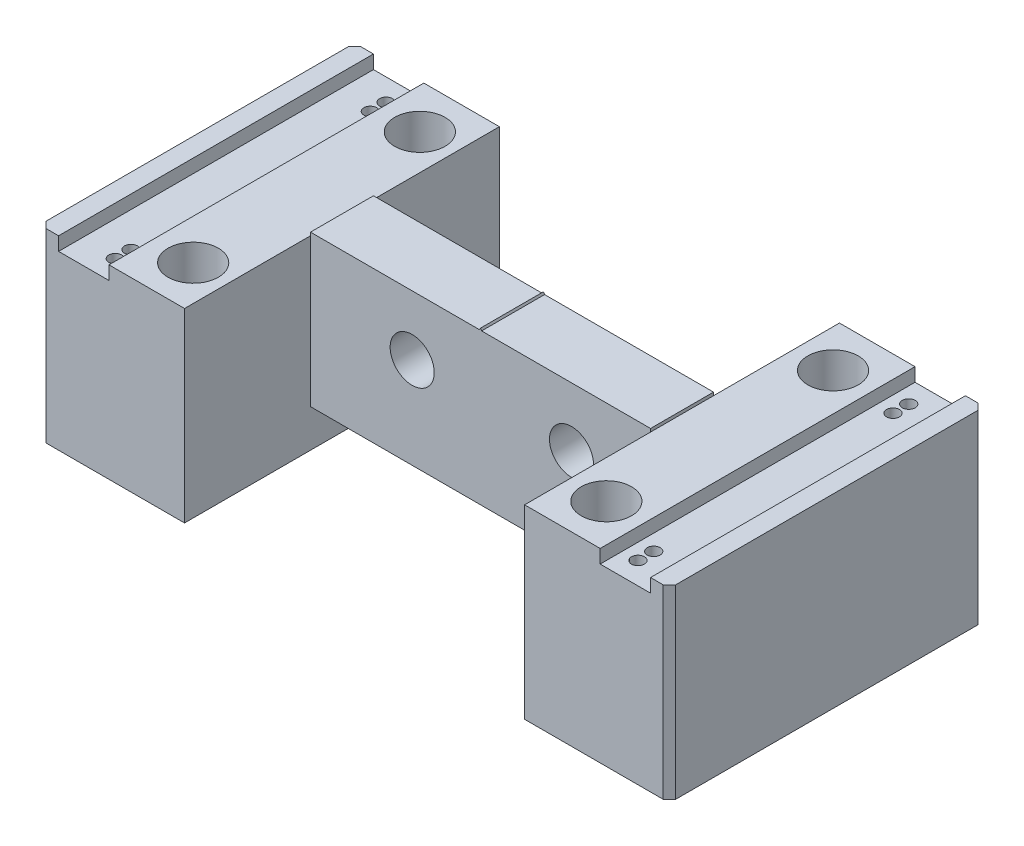
SolidWorks part; units mm, degrees
ref_plane "Front Plane" through (0, 0, 0) normal (0, 0, 1) x (1, 0, 0)
ref_plane "Top Plane" through (0, 0, 0) normal (0, 1, 0) x (1, 0, 0)
ref_plane "Right Plane" through (0, 0, 0) normal (1, 0, 0) x (0, 0, -1)
sketch "Sketch1" plane through (0, 0, 0) normal (0, 0, 1) x (1, 0, 0)
  line L0 (6.0135, 8.1149) -> (9.0135, 8.1149)
  line L1 (-13.9865, 8.1149) -> (-1.9865, 8.1149)
  line L2 (-13.9865, 8.1149) -> (-13.9865, -21.3851)
  line L3 (-13.9865, -21.3851) -> (9.0135, -21.3851)
  line L4 (9.0135, 8.1149) -> (9.0135, -21.3851)
  line L6 (-1.9865, 8.1149) -> (-1.9865, 5.9649)
  line L7 (-1.9865, 5.9649) -> (6.0135, 5.9649)
  line L8 (6.0135, 8.1149) -> (6.0135, 5.9649)
  dimension "D1" = 29.5
  dimension "D2" = 27.35
  dimension "D3" = 23
  dimension "D4" = 8
  dimension "D5" = 12
extrude "Boss-Extrude1" add sketch "Sketch1" along normal blind 50
sketch "Sketch2" plane through (-13.9865, 0, 0) normal (-1, 0, 0) x (0, 0, 1)
  line L0 (50, -21.3851) -> (0, -21.3851) construction
  line L1 (20, -21.3851) -> (30, -21.3851)
  line L2 (20, -21.3851) -> (20, 8.6149)
  line L3 (20, 8.6149) -> (30, 8.6149)
  line L4 (30, -21.3851) -> (30, 8.6149)
  line L5 (0, 8.1149) -> (0, -21.3851) construction
  line L6 (50, 8.1149) -> (50, -21.3851) construction
  dimension "D1" = 20
  dimension "D2" = 20
  dimension "D3" = 30
extrude "Boss-Extrude2" add sketch "Sketch2" along normal blind 54
sketch "Sketch3" plane through (0, 0, 20) normal (0, 0, -1) x (-1, 0, 0)
  line L0 (40.8115, 8.6149) -> (40.9865, 8.918)
  line L1 (67.9865, 8.6149) -> (13.9865, 8.6149) construction
  line L2 (40.9865, 8.918) -> (41.1615, 8.6149)
  line L8 (13.9865, 8.6149) -> (13.9865, 8.1149)
  line L9 (13.9865, 8.1149) -> (13.9865, -21.3851)
  line L10 (13.9865, -21.3851) -> (67.9865, -21.3851)
  line L11 (67.9865, -21.3851) -> (67.9865, 8.6149)
  line L12 (67.9865, 8.6149) -> (13.9865, 8.6149)
  line L17 (41.1615, 8.6149) -> (40.8115, 8.6149)
  point P4 (0, 0)
  point P6 (40.9865, 8.6149)
  point P7 (0, 0)
  dimension "D1" = 60
  dimension "D2" = 0.35
  dimension "D3" = 0
extrude "Boss-Extrude4" add sketch "Sketch3" against normal up to surface (10 mm away) up to face at (-35.5865, -3.4851, 30)
sketch "Sketch4" plane through (0, 0, 0) normal (0, 0, -1) x (-1, 0, 0)
  line L0 (67.9865, 8.6149) -> (67.9865, -21.3851) construction
  line L1 (67.9865, 8.1149) -> (79.9865, 8.1149)
  line L2 (67.9865, 8.1149) -> (67.9865, -21.3851)
  line L3 (67.9865, -21.3851) -> (90.9865, -21.3851)
  line L4 (90.9865, 8.1149) -> (90.9865, -21.3851)
  line L5 (87.9865, 8.1149) -> (90.9865, 8.1149)
  line L7 (79.9865, 8.1149) -> (79.9865, 5.9649)
  line L8 (79.9865, 5.9649) -> (87.9865, 5.9649)
  line L9 (87.9865, 8.1149) -> (87.9865, 5.9649)
  line L10 (-6.0135, 8.1149) -> (-6.0135, 5.9649) construction
  line L11 (-6.0135, 5.9649) -> (1.9865, 5.9649) construction
  line L13 (1.9865, 5.9649) -> (1.9865, 8.1149) construction
  line L14 (1.9865, 8.1149) -> (13.9865, 8.1149) construction
  line L15 (13.9865, -21.3851) -> (-9.0135, -21.3851) construction
  line L16 (-9.0135, -21.3851) -> (-9.0135, 8.1149) construction
  point P13 (0, 0)
extrude "Boss-Extrude5" add sketch "Sketch4" against normal blind 50
sketch "Sketch5" plane through (0, 0, 20) normal (0, 0, -1) x (-1, 0, 0)
  line L0 (67.9865, -21.3851) -> (13.9865, -21.3851) construction
  circle A0 centre (26.5372, -0.8851) radius 3.5
  circle A1 centre (51.8381, -0.8851) radius 3.5
  point P4 (0, 0)
  dimension "D2" = 7
  dimension "D1" = 20.5
extrude "Cut-Extrude1" cut sketch "Sketch5" against normal blind 54
sketch "Sketch6" plane through (0, 8.1149, 0) normal (0, 1, 0) x (1, 0, 0)
  circle A0 centre (-7.9819, -7.0264) radius 2.25
  circle A1 centre (-7.9819, -43.0216) radius 2.25
  circle A2 centre (-73.5937, -43.0216) radius 2.25
  circle A3 centre (-73.5937, -7.0264) radius 2.25
  point P8 (0, 0)
  point P9 (0, 0)
  point P10 (0, 0)
  point P11 (0, 0)
  point P12 (0, 0)
  dimension "D1" = 4.5
extrude "Cut-Extrude2" cut sketch "Sketch6" against normal through all
sketch "Sketch7" plane through (0, 8.1149, 0) normal (0, 1, 0) x (1, 0, 0)
  circle A0 centre (-7.9819, -43.0216) radius 4
  circle A1 centre (-7.9819, -7.0264) radius 4
  circle A2 centre (-73.5937, -43.0216) radius 4
  circle A3 centre (-73.5937, -7.0264) radius 4
  dimension "D1" = 8
extrude "Cut-Extrude3" cut sketch "Sketch7" against normal blind 10
hole_wizard "M2.5 Tapped Hole2" positions "Sketch12" profile "Sketch13" tap size "M2.5" standard "ISO"
sketch "Sketch12" plane through (0, 5.9649, 0) normal (0, 1, 0) x (1, 0, 0)
  line L0 (6.0135, -50) -> (-1.9865, -50) construction
  line L1 (9.0135, -50) -> (9.0135, 0) construction
  point P0 (0.5135, -46.5)
  point P2 (0.5135, -3.5)
  point P4 (-82.4865, -46.5)
  point P6 (-82.4865, -3.5)
  point P12 (0.5135, -44)
  point P14 (0.5135, -6)
  point P16 (-82.4865, -44)
  point P18 (-82.4865, -6)
  point P23 (0, 0)
  point P24 (0, 0)
  point P25 (0, 0)
  point P26 (0, 0)
  dimension "D1" = 3.5
  dimension "D2" = 6
  dimension "D3" = 44
  dimension "D4" = 46.5
  dimension "D5" = 8.5
  dimension "D6" = 91.5
sketch "Sketch13" plane through (0.5135, 5.9649, 46.5) normal (1, 0, 0) x (0, 0, 1)
  line L0 (0, 0) -> (0, 6.9659)
  line L1 (0, 6.9659) -> (1.025, 6.35)
  line L2 (1.025, 6.35) -> (1.025, 0)
  line L5 (1.025, 0) -> (0, 0)
  line L10 (0, 6.9659) -> (-1.025, 6.35) construction
  line L11 (0, -6.35) -> (0, 107.95) construction
  dimension "Tap Drill Dia." = 2.05
  dimension "Tap Drill Depth" = 6.35
  dimension "Drill Angle" = 118
cosmetic thread "Hole Thread5" parameters "D1"=5, "D2"=2.5
cosmetic thread "Hole Thread6" parameters "D1"=5, "D2"=2.5
cosmetic thread "Hole Thread7" parameters "D1"=5, "D2"=2.5
cosmetic thread "Hole Thread8" parameters "D1"=5, "D2"=2.5
cosmetic thread "Hole Thread9" parameters "D1"=5, "D2"=2.5
cosmetic thread "Hole Thread10" parameters "D1"=5, "D2"=2.5
cosmetic thread "Hole Thread11" parameters "D1"=5, "D2"=2.5
cosmetic thread "Hole Thread12" parameters "D1"=5, "D2"=2.5
chamfer "Chamfer1" distance 1 angle 45 4 edges at (-90.9865, -6.6351, 50) (-90.9865, -6.6351, 0) (9.0135, -6.6351, 0) (9.0135, -6.6351, 50)
sketch "Sketch14" plane through (0, 0, 20) normal (0, 0, -1) x (-1, 0, 0)
  line L0 (67.9865, 8.1149) -> (67.9865, -21.3851) construction
  line L1 (13.9865, -21.3851) -> (67.9865, -21.3851)
  line L2 (13.9865, -21.3851) -> (13.9865, -15.3851)
  line L3 (13.9865, -15.3851) -> (67.9865, -15.3851)
  line L4 (67.9865, -21.3851) -> (67.9865, -15.3851)
  dimension "D1" = 6
extrude "Cut-Extrude4" cut sketch "Sketch14" against normal blind 10
